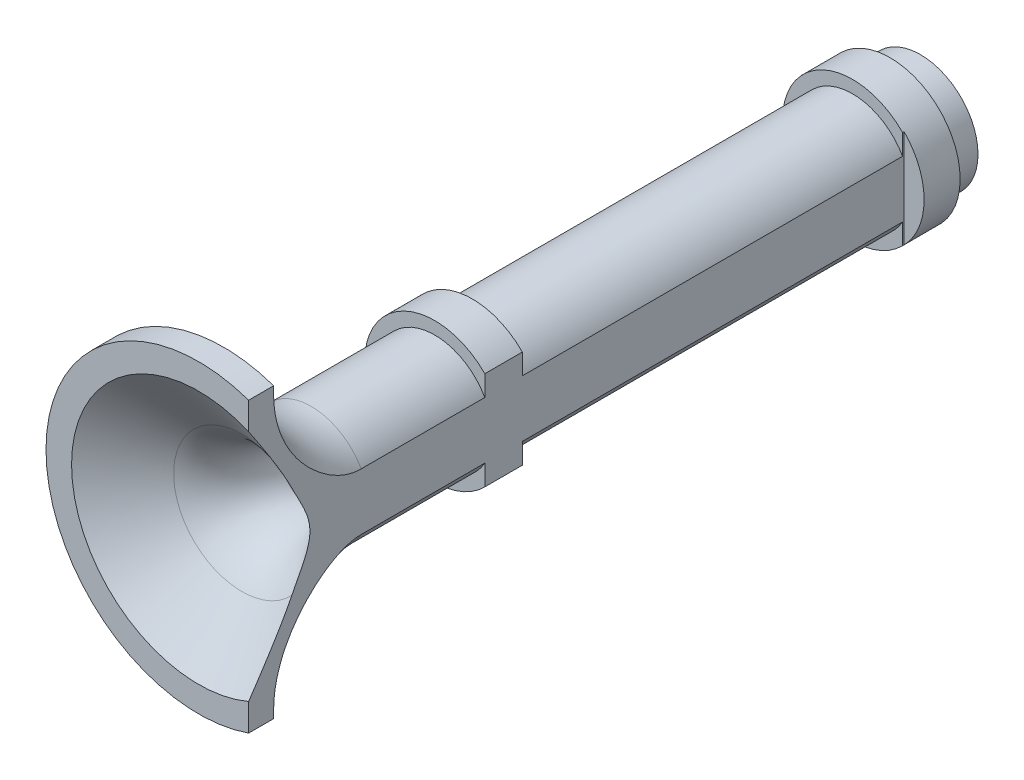
SolidWorks part; units mm, degrees
ref_plane "Спереди" through (0, 0, 0) normal (0, 0, 1) x (1, 0, 0)
ref_plane "Сверху" through (0, 0, 0) normal (0, 1, 0) x (1, 0, 0)
ref_plane "Справа" through (0, 0, 0) normal (1, 0, 0) x (0, 0, -1)
other "Configuration Table"
sketch "Sketch1" plane through (0, 0, 0) normal (1, 0, 0) x (0, 0, -1)
  line L0 (0, 0) -> (15.3, 0) construction
  line L1 (0, 5.0782) -> (0, 6.1)
  line L4 (0, 6.1) -> (1, 6.1)
  line L5 (1, 6.1) -> (1, 5.8)
  line L6 (1.7289, 2.7267) -> (0, 5.0782)
  line L7 (28.8539, 1.3) -> (4.5487, 1.3)
  line L8 (9.4401, 2.3) -> (4.5, 2.3)
  line L9 (28.8539, 1.3) -> (28.8539, 2.3)
  line L14 (28.8539, 2.3) -> (27.6401, 2.3)
  line L15 (27.6401, 2.8) -> (26.1401, 2.8)
  line L16 (28.8539, 2.8) -> (4.5, 2.8) construction
  line L17 (9.4401, 2.3) -> (9.4401, 2.8)
  line L18 (10.9401, 2.3) -> (10.9401, 2.8)
  line L20 (28.8539, 2.3) -> (4.5, 2.3) construction
  line L21 (27.6401, 2.8) -> (27.6401, 2.3)
  line L22 (26.1401, 2.8) -> (26.1401, 2.3)
  line L23 (10.9401, 2.8) -> (9.4401, 2.8)
  line L24 (26.1401, 2.3) -> (10.9401, 2.3)
  line L25 (26.1401, 10.1) -> (26.1401, -1000.5024) construction
  line L26 (27.6401, 10.1) -> (27.6401, -1000.5024) construction
  arc A0 (1, 5.8) -> (4.5, 2.3) centre (4.5, 5.8) ccw
  arc A1 (1.7289, 2.7267) -> (4.5487, 1.3) centre (4.5487, 4.8) ccw
  point P5 (9.4401, -1003.5024)
  point P6 (0, 0)
  point P8 (9.4401, 1010.1)
  point P9 (15.3, 0)
  point P22 (10.9401, -1003.5024)
  point P23 (10.9401, 1010.1)
  dimension "D1" = 3.5
  dimension "D3" = 3.5
  dimension "D2" = 0.5
  dimension "D4" = 1.5
revolve "Revolve1" add sketch "Sketch1" angle 360 about L0
sketch "Sketch2" plane through (0, 0, 0) normal (0, 0, 1) x (1, 0, 0)
  line L0 (2, 6) -> (2, -6.569)
  line L1 (2, -6.569) -> (7.8192, -6.569)
  line L2 (7.8192, -6.569) -> (7.708, 5.9581)
  line L3 (7.708, 5.9581) -> (2, 6)
extrude "Cut-Extrude1" cut sketch "Sketch2" against normal blind 26.2
